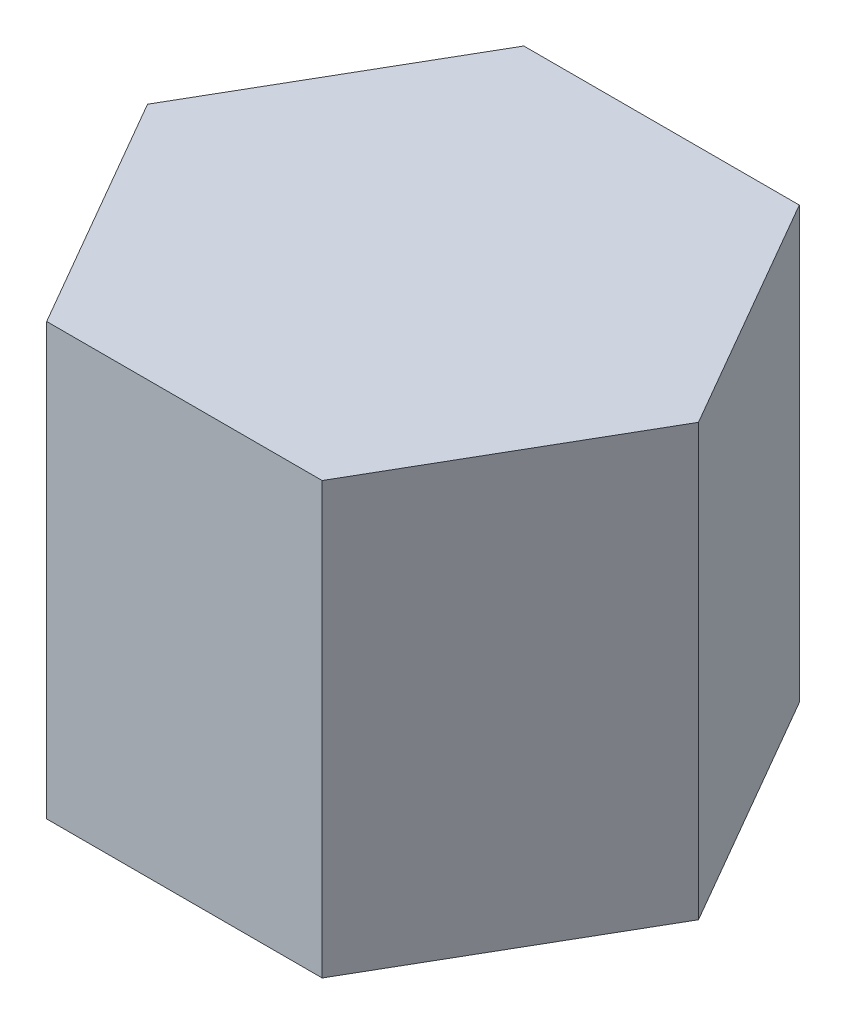
SolidWorks part; units mm, degrees
ref_plane "Front" through (0, 0, 0) normal (0, 0, 1) x (1, 0, 0)
ref_plane "Top" through (0, 0, 0) normal (0, 1, 0) x (1, 0, 0)
ref_plane "Right" through (0, 0, 0) normal (1, 0, 0) x (0, 0, -1)
sketch "Sketch1" plane through (0, 0, 0) normal (0, 1, 0) x (1, 0, 0)
  line L1 (25.5766, -44.3) -> (51.1532, 0)
  line L2 (51.1532, 0) -> (25.5766, 44.3)
  line L3 (25.5766, 44.3) -> (-25.5766, 44.3)
  line L4 (-25.5766, 44.3) -> (-51.1532, 0)
  line L5 (-51.1532, 0) -> (-25.5766, -44.3)
  line L6 (-25.5766, -44.3) -> (25.5766, -44.3)
  circle A0 centre (0, 0) radius 44.3 construction
  dimension "D1" = 88.6
extrude "Boss-Extrude1" add sketch "Sketch1" against normal blind 80
